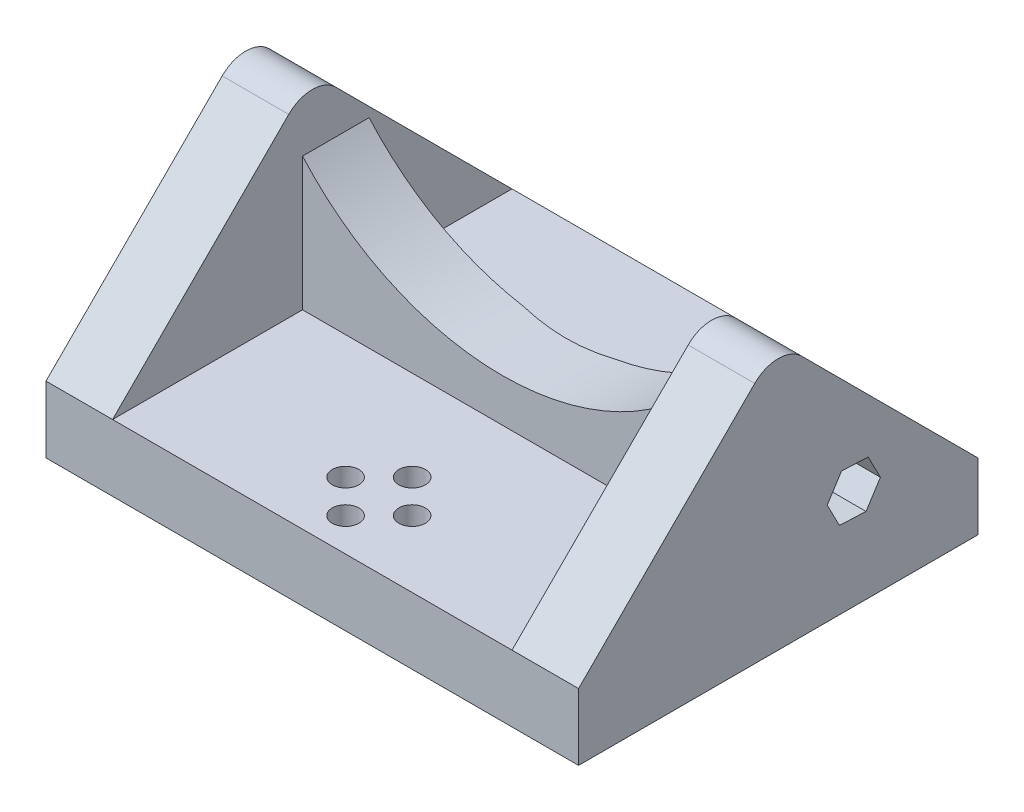
SolidWorks part; units mm, degrees
ref_plane "Front Plane" through (0, 0, 0) normal (0, 0, 1) x (1, 0, 0)
ref_plane "Top Plane" through (0, 0, 0) normal (0, 1, 0) x (1, 0, 0)
ref_plane "Right Plane" through (0, 0, 0) normal (1, 0, 0) x (0, 0, -1)
sketch "Sketch1" plane through (0, 0, 0) normal (0, 1, 0) x (1, 0, 0)
  line L1 (0, 0) -> (-80, 0)
  line L2 (0, 0) -> (0, 60)
  line L3 (0, 60) -> (-80, 60)
  line L4 (-80, 0) -> (-80, 60)
  dimension "D1" = 80
  dimension "D2" = 60
extrude "Boss-Extrude1" add sketch "Sketch1" along normal blind 10
sketch "Sketch2" plane through (0, 0, 0) normal (1, 0, 0) x (0, 0, -1)
  line L0 (0, 10) -> (30, 40)
  line L1 (30, 40) -> (60, 10)
  line L2 (60, 10) -> (0, 10)
  point P5 (0, 0)
  point P6 (0, 0)
  point P7 (30, 10)
  point P8 (0, 0)
  dimension "D1" = 45
extrude "Boss-Extrude2" add sketch "Sketch2" against normal blind 10
pattern_linear "LPattern2" count 2 spacing 70 along (-1, 0, 0) of "Boss-Extrude2"
fillet "Fillet1" radius 5 2 edges at (-5, 40, -30) (-75, 40, -30)
sketch "Sketch3" plane through (0, 0, 0) normal (0, 0, 1) x (1, 0, 0)
  line L0 (-70, 36.4645) -> (-70, 10) construction
  line L1 (-10, 36.4645) -> (-10, 10) construction
  line L2 (-70, 30) -> (-70, 10)
  line L3 (-70, 10) -> (-10, 10) construction
  line L4 (-70, 10) -> (-10, 10)
  line L5 (-10, 10) -> (-10, 30)
  arc A0 (-70, 30) -> (-10, 30) centre (-40, 56.4575) ccw
  dimension "D1" = 40
  dimension "D2" = 20
extrude "Boss-Extrude3" add sketch "Sketch3" along normal mid plane 10 from vertex at -33.5355 starting at point (-70, 36.4645, -33.5355)
sketch "Sketch4" plane through (0, 10, 0) normal (0, 1, 0) x (1, 0, 0)
  line L0 (-80, 26.4645) -> (-80, 0) construction
  line L1 (-70, 0) -> (-10, 0) construction
  circle A0 centre (-40, 10) radius 5 construction
  circle A1 centre (-40, 15) radius 2
  circle A2 centre (-35, 10) radius 2
  circle A3 centre (-40, 5) radius 2
  circle A4 centre (-45, 10) radius 2
  point P17 (-40, 10)
  dimension "D3" = 10
  dimension "D4" = 4
  dimension "D1" = 40
  dimension "D2" = 10
  dimension "D5" = 4
extrude "Cut-Extrude1" cut sketch "Sketch4" against normal through all
sketch "Sketch5" plane through (0, 0, 0) normal (1, 0, 0) x (0, 0, -1)
  line L0 (0, 0) -> (60, 0) construction
  line L1 (43.1842, 11.449) -> (45.3388, 14.8191)
  line L2 (45.3388, 14.8191) -> (43.4976, 18.3701)
  line L3 (43.4976, 18.3701) -> (39.5017, 18.551)
  line L4 (39.5017, 18.551) -> (37.347, 15.1809)
  line L5 (37.347, 15.1809) -> (39.1883, 11.6299)
  line L6 (39.1883, 11.6299) -> (43.1842, 11.449)
  circle A0 centre (41.3429, 15) radius 3.4641 construction
  arc A3 (33.5355, 36.4645) -> (26.4645, 36.4645) centre (30, 32.9289) ccw construction
  point P13 (30, 37.9289)
  point P15 (0, 0)
  dimension "D2" = 4
  dimension "D1" = 15
  dimension "D3" = 18.9283
  dimension "D4" = 37.347
extrude "Cut-Extrude2" cut sketch "Sketch5" against normal through all
